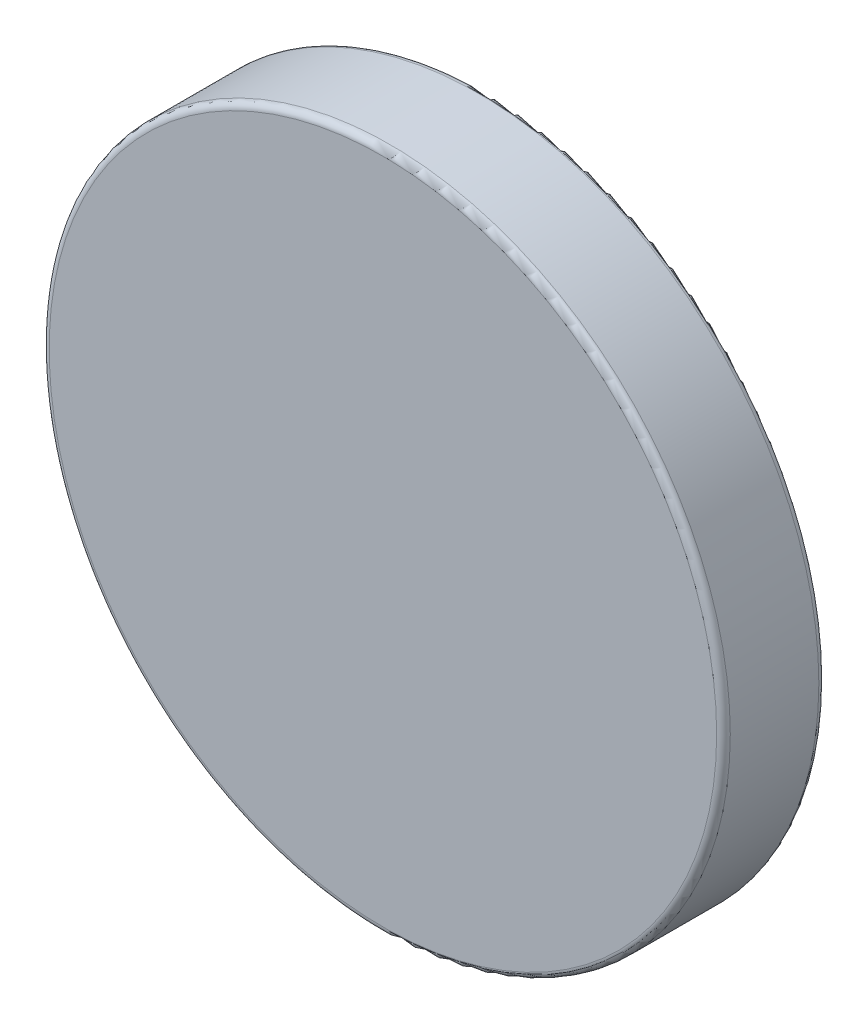
SolidWorks part; units mm, degrees
ref_plane "前视基准面" through (0, 0, 0) normal (0, 0, 1) x (1, 0, 0)
ref_plane "上视基准面" through (0, 0, 0) normal (0, 1, 0) x (1, 0, 0)
ref_plane "右视基准面" through (0, 0, 0) normal (1, 0, 0) x (0, 0, -1)
sketch "草图1" plane through (0, 0, 0) normal (0, 0, 1) x (1, 0, 0)
  circle A0 centre (0, 0) radius 10
  dimension "D1" = 20
extrude "凸台-拉伸1" add sketch "草图1" along normal blind 3
fillet "圆角1" radius 0.2 2 edges at (10, 0, 0) (10, 0, 3)
